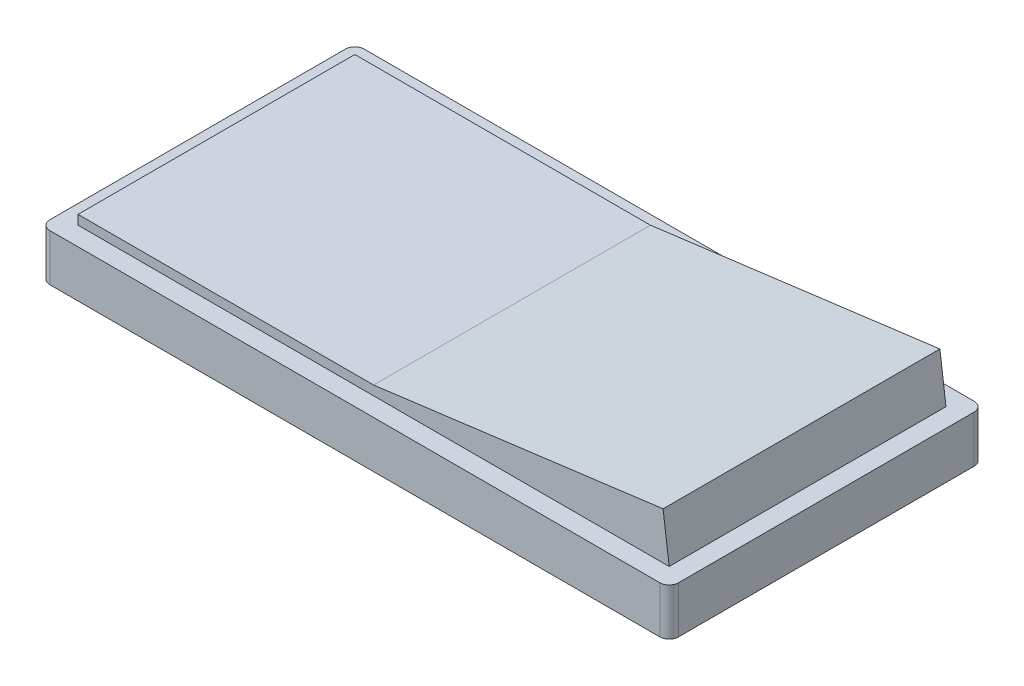
SolidWorks part; units mm, degrees
ref_plane "Front Plane" through (0, 0, 0) normal (0, 0, 1) x (1, 0, 0)
ref_plane "Top Plane" through (0, 0, 0) normal (0, 1, 0) x (1, 0, 0)
ref_plane "Right Plane" through (0, 0, 0) normal (1, 0, 0) x (0, 0, -1)
sketch "Sketch1" plane through (0, 0, 0) normal (0, 1, 0) x (1, 0, 0)
  line L1 (-33.5, -16.75) -> (33.5, -16.75)
  line L2 (-33.5, -16.75) -> (-33.5, 16.75)
  line L3 (-33.5, 16.75) -> (33.5, 16.75)
  line L4 (33.5, -16.75) -> (33.5, 16.75)
  line L5 (-33.5, -16.75) -> (33.5, 16.75) construction
  line L6 (-33.5, 16.75) -> (33.5, -16.75) construction
  point P0 (0, 0)
  dimension "D1" = 33.5
  dimension "D2" = 67
extrude "Boss-Extrude1" add sketch "Sketch1" along normal blind 5
fillet "Fillet1" radius 1 4 edges at (-33.5, 2.5, 16.75) (33.5, 2.5, 16.75) (33.5, 2.5, -16.75) (-33.5, 2.5, -16.75)
sketch "Sketch2" plane through (0, 5, 0) normal (0, 1, 0) x (1, 0, 0)
  line L8 (-31.5, 14.75) -> (-31.5, -14.75)
  line L9 (-31.5, -14.75) -> (31.5, -14.75)
  line L10 (31.5, -14.75) -> (31.5, 14.75)
  line L11 (31.5, 14.75) -> (-31.5, 14.75)
  line L12 (-31.5, 14.75) -> (-31.5, -14.75)
  line L13 (-31.5, -14.75) -> (31.5, -14.75)
  line L14 (31.5, -14.75) -> (31.5, 14.75)
  line L15 (31.5, 14.75) -> (-31.5, 14.75)
  dimension "D1" = 2
extrude "Boss-Extrude2" add sketch "Sketch2" along normal blind 5
sketch "Sketch3" plane through (0, 0, 14.75) normal (0, 0, 1) x (1, 0, 0)
  line L0 (0, 6) -> (30.8517, 10)
  line L2 (30.8517, 10) -> (31.5, 5)
  line L3 (-31.5, 6) -> (0, 6)
  line L4 (-31.5, 10) -> (-31.5, 5) construction
  line L5 (-31.5, 5) -> (31.5, 5) construction
  line L6 (-31.5, 10) -> (31.5, 10) construction
  point P2 (0, 5.5313)
  point P10 (0, 0)
  point P11 (0, 5)
  point P12 (0, 5.6964)
  point P13 (30.8576, 10)
  dimension "D1" = 1
  dimension "D2" = 90
extrude "Cut-Extrude1" cut sketch "Sketch3" against normal through all and the other way through all
